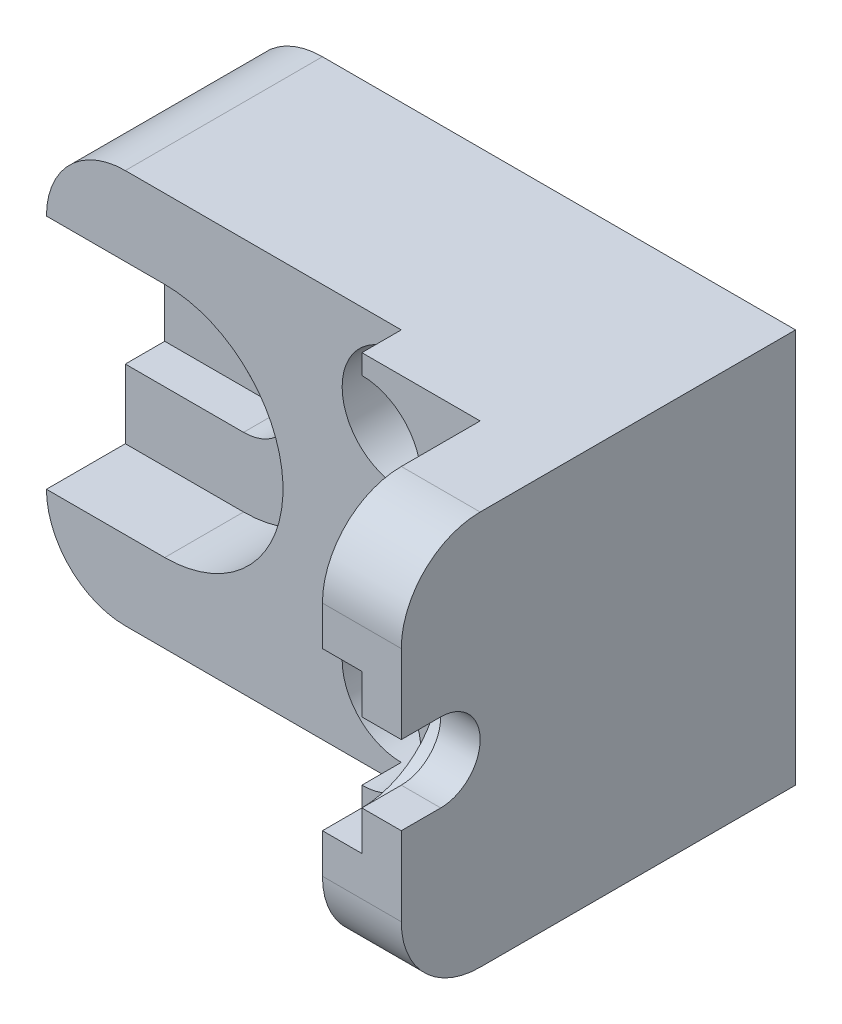
SolidWorks part; units mm, degrees
ref_plane "Front" through (0, 0, 0) normal (0, 0, 1) x (1, 0, 0)
ref_plane "Top" through (0, 0, 0) normal (0, 1, 0) x (1, 0, 0)
ref_plane "Right" through (0, 0, 0) normal (1, 0, 0) x (0, 0, -1)
sketch "Sketch1" plane through (0, 0, 0) normal (0, 0, 1) x (1, 0, 0)
  line L1 (2, 0) -> (14, 0)
  line L2 (0, 2) -> (0, 8)
  line L3 (2, 10) -> (14, 10)
  line L4 (14, 0) -> (14, 10)
  arc A0 (0, 8) -> (2, 10) centre (2, 8) cw
  arc A1 (2, 0) -> (0, 2) centre (2, 2) cw
  circle A2 centre (3, 5) radius 1.25
  circle A3 centre (9, 8) radius 0.5
  circle A4 centre (9, 2) radius 0.5
  point P7 (0, 10)
  point P10 (0, 0)
  dimension "D3" = 2
  dimension "D4" = 2.5
  dimension "D7" = 1
  dimension "D9" = 1
  dimension "D1" = 10
  dimension "D2" = 14
  dimension "D5" = 5
  dimension "D6" = 3
  dimension "D8" = 5
extrude "Boss-Extrude1" add sketch "Sketch1" along normal blind 6
sketch "Sketch2" plane through (14, 0, 0) normal (1, 0, 0) x (0, 0, -1)
  line L0 (-9, 5) -> (-12.2788, 5) construction
  line L1 (-6, 10) -> (-8, 10)
  line L2 (-6, 10) -> (-6, 0)
  line L3 (-6, 0) -> (-8, 0)
  line L4 (-10, 8) -> (-10, 7)
  line L5 (-9, 4) -> (-10, 4)
  line L6 (-9, 6) -> (-10, 6)
  line L7 (-9, 5) -> (-12.2788, 5) construction
  line L8 (-9, 3) -> (-10, 3)
  line L9 (-9, 7) -> (-10, 7)
  line L10 (-10, 6) -> (-10, 2)
  line L11 (-10, 7) -> (-10, 3)
  arc A0 (-8, 0) -> (-10, 2) centre (-8, 2) cw
  arc A1 (-8, 10) -> (-10, 8) centre (-8, 8) ccw
  arc A2 (-9, 4) -> (-9, 6) centre (-9, 5) ccw
  arc A4 (-9, 3) -> (-9, 7) centre (-9, 5) ccw
  point P9 (-10, 10)
  point P12 (-10.6394, 5)
  point P17 (-10.6394, 5)
  line M9 (-6, 10) -> (-6, 0)
  dimension "D2" = 2
  dimension "D4" = 1
  dimension "D5" = 2
  dimension "D1" = 4
  dimension "D3" = 1
extrude "Boss-Extrude2" add sketch "Sketch2" against normal blind 2 contours A4 L8 L10 A0 L3 L1 A1 L4 L9 M9 | L8 A4 L9 L11 L6 A2 L5 L10
sketch "Sketch5" plane through (12, 0, 0) normal (-1, 0, 0) x (0, 0, 1)
  line L0 (9, 5) -> (11.1679, 5) construction
  line L1 (9, 7) -> (11.1679, 7)
  line L2 (9, 3) -> (11.1679, 3)
  arc A0 (9, 7) -> (9, 3) centre (9, 5) ccw
  arc A1 (11.1679, 3) -> (11.1679, 7) centre (11.1679, 5) ccw
  point P3 (10.084, 5)
  dimension "D1" = 2
extrude "Cut-Extrude1" cut sketch "Sketch5" against normal blind 1
sketch "Sketch6" plane through (0, 0, 6) normal (0, 0, 1) x (1, 0, 0)
  line L1 (9, 10.1156) -> (9, 9.5)
  line L2 (9, 6.5) -> (9, 3.5)
  line L3 (9, 0.5) -> (9, -0.3365)
  line L4 (9, -0.3365) -> (-3.1112, -0.3365)
  line L5 (-3.1112, -0.3365) -> (-3.1112, 10.1156)
  line L6 (-3.1112, 10.1156) -> (9, 10.1156)
  arc A0 (9, 6.5) -> (9, 9.5) centre (9, 8) ccw
  arc A1 (9, 0.5) -> (9, 3.5) centre (9, 2) ccw
  dimension "D1" = 3
  dimension "D2" = 3
extrude "Cut-Extrude2" cut sketch "Sketch6" against normal blind 1
sketch "Sketch7" plane through (0, 0, 5) normal (0, 0, 1) x (1, 0, 0)
  line L0 (3, 5) -> (-3.2488, 5) construction
  line L1 (3, 2) -> (-3.2488, 2)
  line L2 (3, 8) -> (-3.2488, 8)
  arc A0 (3, 2) -> (3, 8) centre (3, 5) ccw
  arc A1 (-3.2488, 8) -> (-3.2488, 2) centre (-3.2488, 5) ccw
  point P3 (-0.1244, 5)
  dimension "D1" = 3
extrude "Cut-Extrude3" cut sketch "Sketch7" against normal blind 2
sketch "Sketch8" plane through (0, 0, 3) normal (0, 0, 1) x (1, 0, 0)
  line L0 (3, 5) -> (-1.5624, 5) construction
  line L1 (3, 3.75) -> (-1.5624, 3.75)
  line L2 (3, 6.25) -> (-1.5624, 6.25)
  arc A0 (3, 3.75) -> (3, 6.25) centre (3, 5) ccw
  arc A1 (-1.5624, 6.25) -> (-1.5624, 3.75) centre (-1.5624, 5) ccw
  point P3 (0.7188, 5)
  dimension "D1" = 1.25
extrude "Cut-Extrude4" cut sketch "Sketch8" against normal blind 1
sketch "Sketch9" plane through (0, 0, 5) normal (0, 0, 1) x (1, 0, 0)
  circle A0 centre (9, 8) radius 1.5
  circle A1 centre (9, 2) radius 1.5
extrude "Cut-Extrude5" cut sketch "Sketch9" against normal blind 3
